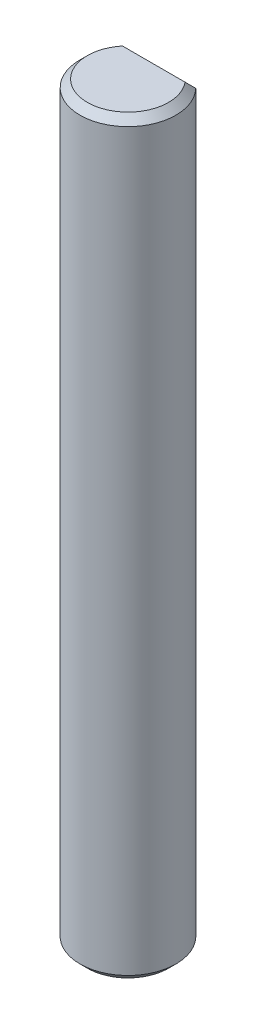
SolidWorks part; units mm, degrees
ref_plane "Front Plane" through (0, 0, 0) normal (0, 0, 1) x (1, 0, 0)
ref_plane "Top Plane" through (0, 0, 0) normal (0, 1, 0) x (1, 0, 0)
ref_plane "Right Plane" through (0, 0, 0) normal (1, 0, 0) x (0, 0, -1)
sketch "Sketch1" plane through (0, 0, 0) normal (0, 1, 0) x (1, 0, 0)
  line L0 (-2.3452, 2.25) -> (2.3452, 2.25)
  circle A0 centre (0, 0) radius 3.25 construction
  arc A1 (-2.3452, 2.25) -> (2.3452, 2.25) centre (0, 0) ccw
  point P5 (0, -3.25)
  dimension "D2" = 6.5
  dimension "D1" = 5.5
extrude "Boss-Extrude1" add sketch "Sketch1" along normal mid plane 50.8
chamfer "Chamfer1" distance 0.5 angle 45 4 edges at (0, -25.4, -2.25) (0, -25.4, 3.25) (0, 25.4, -2.25) (0, 25.4, 3.25)
